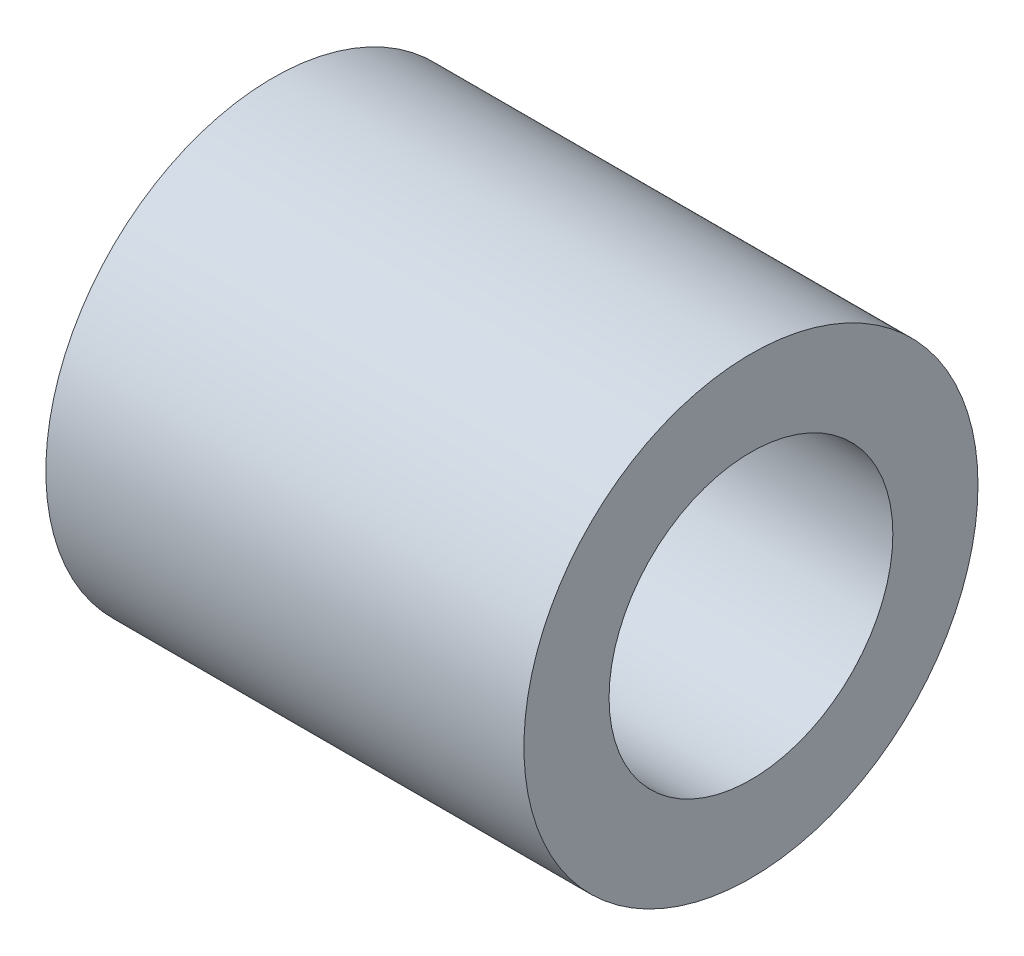
SolidWorks part; units mm, degrees
material "Silicon Rubber"
ref_plane "Front Plane" through (0, 0, 0) normal (0, 0, 1) x (1, 0, 0)
ref_plane "Top Plane" through (0, 0, 0) normal (0, 1, 0) x (1, 0, 0)
ref_plane "Right Plane" through (0, 0, 0) normal (1, 0, 0) x (0, 0, -1)
sketch "Sketch1" plane through (0, 0, 0) normal (1, 0, 0) x (0, 0, -1)
  circle A0 centre (0, 0) radius 4
  dimension "D1" = 8
extrude "Boss-Extrude1" add sketch "Sketch1" along normal blind 9
chamfer "Chamfer1" distance 1 angle 30 1 edges at (0, 0, -4)
sketch "Sketch2" plane through (9, 0, 0) normal (1, 0, 0) x (0, 0, -1)
  circle A0 centre (0, 0) radius 2.5
extrude "Cut-Extrude1" cut sketch "Sketch2" against normal blind 6
